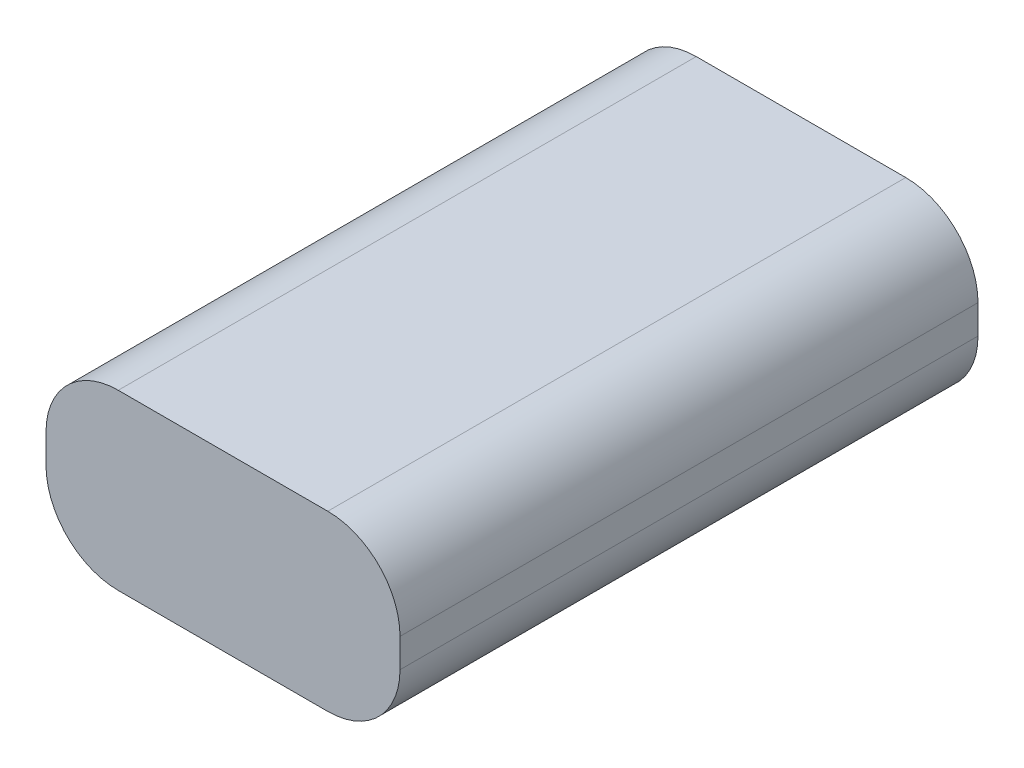
SolidWorks part; units mm, degrees
ref_plane "Ebene vorne" through (0, 0, 0) normal (0, 0, 1) x (1, 0, 0)
ref_plane "Ebene oben" through (0, 0, 0) normal (0, 1, 0) x (1, 0, 0)
ref_plane "Ebene rechts" through (0, 0, 0) normal (1, 0, 0) x (0, 0, -1)
sketch "Skizze1" plane through (0, 0, 0) normal (0, 0, 1) x (1, 0, 0)
  line L1 (0, 0) -> (49, 0)
  line L2 (0, 0) -> (0, 24)
  line L3 (0, 24) -> (49, 24)
  line L4 (49, 0) -> (49, 24)
  dimension "D1" = 49
  dimension "D2" = 24
extrude "Aufsatz-Linear austragen1" add sketch "Skizze1" along normal blind 80
fillet "Verrundung1" radius 10 4 edges at (0, 0, 40) (0, 24, 40) (49, 0, 40) (49, 24, 40)
